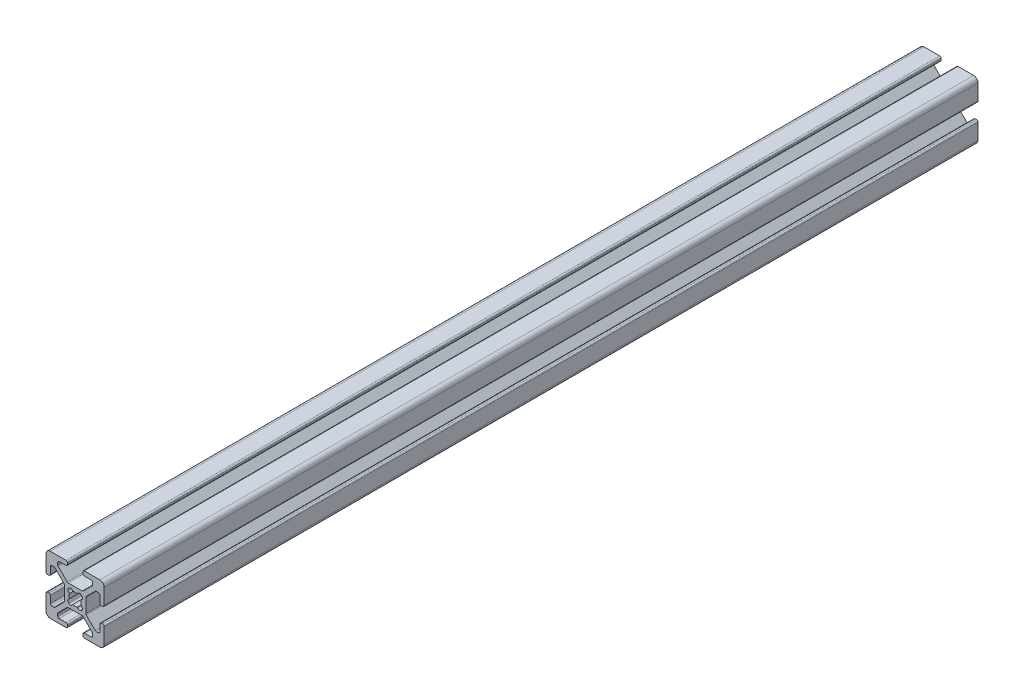
SolidWorks part; units mm, degrees
material "6063-O, Barre extrudée (SS)"
ref_plane "Front Plane" through (0, 0, 0) normal (0, 0, 1) x (1, 0, 0)
ref_plane "Top Plane" through (0, 0, 0) normal (0, 1, 0) x (1, 0, 0)
ref_plane "Right Plane" through (0, 0, 0) normal (1, 0, 0) x (0, 0, -1)
sketch "Sketch1" plane through (0, 0, 0) normal (0, 0, 1) x (1, 0, 0)
  line L0 (-5.0323, -0.3411) -> (-5.5163, -0.3411)
  line L1 (-6.0243, 0.1669) -> (-6.0243, 2.5159)
  line L2 (-4.5243, 0.1669) -> (-4.5243, 5.5289)
  line L3 (-10.8693, -5.355) -> (-10.8693, -0.5871)
  line L4 (-7.2582, 3.0239) -> (-6.5323, 3.0239)
  line L5 (-7.6174, 2.8752) -> (-10.7205, -0.2279)
  line L6 (-5.0323, -5.6011) -> (-5.5163, -5.6011)
  line L7 (-4.5243, -6.1091) -> (-4.5243, -11.4711)
  line L8 (-6.0243, -6.1091) -> (-6.0243, -8.4581)
  line L9 (-7.2582, -8.9661) -> (-6.5323, -8.9661)
  line L10 (-7.6174, -8.8173) -> (-10.7205, -5.7142)
  line L11 (-12.3994, -5.2756) -> (-12.2198, -5.096)
  line L12 (-17.1543, 6.5209) -> (-17.1543, 6.0369)
  line L13 (-17.6623, 7.0289) -> (-23.0243, 7.0289)
  line L14 (-17.6623, 5.5289) -> (-20.0113, 5.5289)
  line L15 (-12.1404, 0.6839) -> (-16.9082, 0.6839)
  line L16 (-20.5193, 4.295) -> (-20.5193, 5.0209)
  line L17 (-20.3705, 3.9358) -> (-17.2674, 0.8327)
  line L18 (-11.8943, 6.5209) -> (-11.8943, 6.0369)
  line L19 (-11.3863, 7.0289) -> (-6.0243, 7.0289)
  line L20 (-11.3863, 5.5289) -> (-9.0373, 5.5289)
  line L21 (-8.5293, 4.295) -> (-8.5293, 5.0209)
  line L22 (-8.6781, 3.9358) -> (-11.7812, 0.8327)
  line L23 (-12.2198, -0.8462) -> (-12.3994, -0.6666)
  line L24 (-24.0163, -5.6011) -> (-23.5323, -5.6011)
  line L25 (-24.5243, -6.1091) -> (-24.5243, -11.4711)
  line L26 (-23.0243, -6.1091) -> (-23.0243, -8.4581)
  line L27 (-18.1793, -0.5871) -> (-18.1793, -5.355)
  line L28 (-21.7904, -8.9661) -> (-22.5163, -8.9661)
  line L29 (-21.4312, -8.8173) -> (-18.3281, -5.7142)
  line L30 (-24.0163, -0.3411) -> (-23.5323, -0.3411)
  line L31 (-24.5243, 0.1669) -> (-24.5243, 5.5289)
  line L32 (-23.0243, 0.1669) -> (-23.0243, 2.5159)
  line L33 (-21.7904, 3.0239) -> (-22.5163, 3.0239)
  line L34 (-21.4312, 2.8752) -> (-18.3281, -0.2279)
  line L35 (-16.6492, -0.6666) -> (-16.8288, -0.8462)
  line L36 (-11.8943, -12.4631) -> (-11.8943, -11.9791)
  line L37 (-11.3863, -12.9711) -> (-6.0243, -12.9711)
  line L38 (-11.3863, -11.4711) -> (-9.0373, -11.4711)
  line L39 (-16.9082, -6.6261) -> (-12.1404, -6.6261)
  line L40 (-8.5293, -10.2371) -> (-8.5293, -10.9631)
  line L41 (-8.6781, -9.8779) -> (-11.7812, -6.7748)
  line L42 (-17.1543, -12.4631) -> (-17.1543, -11.9791)
  line L43 (-17.6623, -12.9711) -> (-23.0243, -12.9711)
  line L44 (-17.6623, -11.4711) -> (-20.0113, -11.4711)
  line L45 (-20.5193, -10.2371) -> (-20.5193, -10.9631)
  line L46 (-20.3705, -9.8779) -> (-17.2674, -6.7748)
  line L47 (-16.8288, -5.096) -> (-16.6492, -5.2756)
  arc A0 (-15.3283, -4.9062) -> (-13.7203, -4.9062) centre (-14.5243, -2.9711) ccw
  arc A1 (-6.0243, 2.5159) -> (-6.5323, 3.0239) centre (-6.5323, 2.5159) ccw
  arc A2 (-7.2582, 3.0239) -> (-7.6174, 2.8752) centre (-7.2582, 2.5159) ccw
  arc A3 (-10.7205, -0.2279) -> (-10.8693, -0.5871) centre (-10.3613, -0.5871) ccw
  arc A4 (-10.8693, -5.355) -> (-10.7205, -5.7142) centre (-10.3613, -5.355) ccw
  arc A5 (-7.6174, -8.8173) -> (-7.2582, -8.9661) centre (-7.2582, -8.4581) ccw
  arc A6 (-6.5323, -8.9661) -> (-6.0243, -8.4581) centre (-6.5323, -8.4581) ccw
  arc A7 (-5.5163, -5.6011) -> (-6.0243, -6.1091) centre (-5.5163, -6.1091) ccw
  arc A8 (-4.5243, -6.1091) -> (-5.0323, -5.6011) centre (-5.0323, -6.1091) ccw
  arc A9 (-5.0323, -0.3411) -> (-4.5243, 0.1669) centre (-5.0323, 0.1669) ccw
  arc A10 (-6.0243, 0.1669) -> (-5.5163, -0.3411) centre (-5.5163, 0.1669) ccw
  arc A11 (-13.7203, -4.9062) -> (-12.3994, -5.2756) centre (-12.9559, -4.7191) ccw
  arc A12 (-12.2198, -5.096) -> (-12.5892, -3.775) centre (-12.7763, -4.5395) ccw
  arc A13 (-17.1543, 6.5209) -> (-17.6623, 7.0289) centre (-17.6623, 6.5209) ccw
  arc A14 (-17.6623, 5.5289) -> (-17.1543, 6.0369) centre (-17.6623, 6.0369) ccw
  arc A15 (-12.5892, -3.775) -> (-12.5892, -2.1671) centre (-14.5243, -2.9711) ccw
  arc A16 (-17.2674, 0.8327) -> (-16.9082, 0.6839) centre (-16.9082, 1.1919) ccw
  arc A17 (-20.0113, 5.5289) -> (-20.5193, 5.0209) centre (-20.0113, 5.0209) ccw
  arc A18 (-20.5193, 4.295) -> (-20.3705, 3.9358) centre (-20.0113, 4.295) ccw
  arc A19 (-11.8943, 6.0369) -> (-11.3863, 5.5289) centre (-11.3863, 6.0369) ccw
  arc A20 (-11.3863, 7.0289) -> (-11.8943, 6.5209) centre (-11.3863, 6.5209) ccw
  arc A21 (-8.5293, 5.0209) -> (-9.0373, 5.5289) centre (-9.0373, 5.0209) ccw
  arc A22 (-8.6781, 3.9358) -> (-8.5293, 4.295) centre (-9.0373, 4.295) ccw
  arc A23 (-12.1404, 0.6839) -> (-11.7812, 0.8327) centre (-12.1404, 1.1919) ccw
  arc A24 (-12.5892, -2.1671) -> (-12.2198, -0.8462) centre (-12.7763, -1.4027) ccw
  arc A25 (-12.3994, -0.6666) -> (-13.7203, -1.0359) centre (-12.9559, -1.223) ccw
  arc A26 (-24.0163, -5.6011) -> (-24.5243, -6.1091) centre (-24.0163, -6.1091) ccw
  arc A27 (-23.0243, -6.1091) -> (-23.5323, -5.6011) centre (-23.5323, -6.1091) ccw
  arc A28 (-13.7203, -1.0359) -> (-15.3283, -1.0359) centre (-14.5243, -2.9711) ccw
  arc A29 (-18.3281, -5.7142) -> (-18.1793, -5.355) centre (-18.6873, -5.355) ccw
  arc A30 (-23.0243, -8.4581) -> (-22.5163, -8.9661) centre (-22.5163, -8.4581) ccw
  arc A31 (-21.7904, -8.9661) -> (-21.4312, -8.8173) centre (-21.7904, -8.4581) ccw
  arc A32 (-23.5323, -0.3411) -> (-23.0243, 0.1669) centre (-23.5323, 0.1669) ccw
  arc A33 (-24.5243, 0.1669) -> (-24.0163, -0.3411) centre (-24.0163, 0.1669) ccw
  arc A34 (-22.5163, 3.0239) -> (-23.0243, 2.5159) centre (-22.5163, 2.5159) ccw
  arc A35 (-21.4312, 2.8752) -> (-21.7904, 3.0239) centre (-21.7904, 2.5159) ccw
  arc A36 (-18.1793, -0.5871) -> (-18.3281, -0.2279) centre (-18.6873, -0.5871) ccw
  arc A37 (-15.3283, -1.0359) -> (-16.6492, -0.6666) centre (-16.0927, -1.223) ccw
  arc A38 (-16.8288, -0.8462) -> (-16.4594, -2.1671) centre (-16.2723, -1.4027) ccw
  arc A39 (-11.8943, -12.4631) -> (-11.3863, -12.9711) centre (-11.3863, -12.4631) ccw
  arc A40 (-11.3863, -11.4711) -> (-11.8943, -11.9791) centre (-11.3863, -11.9791) ccw
  arc A41 (-16.4594, -2.1671) -> (-16.4594, -3.775) centre (-14.5243, -2.9711) ccw
  arc A42 (-11.7812, -6.7748) -> (-12.1404, -6.6261) centre (-12.1404, -7.1341) ccw
  arc A43 (-9.0373, -11.4711) -> (-8.5293, -10.9631) centre (-9.0373, -10.9631) ccw
  arc A44 (-8.5293, -10.2371) -> (-8.6781, -9.8779) centre (-9.0373, -10.2371) ccw
  arc A45 (-17.1543, -11.9791) -> (-17.6623, -11.4711) centre (-17.6623, -11.9791) ccw
  arc A46 (-17.6623, -12.9711) -> (-17.1543, -12.4631) centre (-17.6623, -12.4631) ccw
  arc A47 (-20.5193, -10.9631) -> (-20.0113, -11.4711) centre (-20.0113, -10.9631) ccw
  arc A48 (-20.3705, -9.8779) -> (-20.5193, -10.2371) centre (-20.0113, -10.2371) ccw
  arc A49 (-16.9082, -6.6261) -> (-17.2674, -6.7748) centre (-16.9082, -7.1341) ccw
  arc A50 (-16.4594, -3.775) -> (-16.8288, -5.096) centre (-16.2723, -4.5395) ccw
  arc A51 (-16.6492, -5.2756) -> (-15.3283, -4.9062) centre (-16.0927, -4.7191) ccw
  arc A52 (-4.5243, 5.5289) -> (-6.0243, 7.0289) centre (-6.0243, 5.5289) ccw
  arc A53 (-6.0243, -12.9711) -> (-4.5243, -11.4711) centre (-6.0243, -11.4711) ccw
  arc A54 (-24.5243, -11.4711) -> (-23.0243, -12.9711) centre (-23.0243, -11.4711) ccw
  arc A55 (-23.0243, 7.0289) -> (-24.5243, 5.5289) centre (-23.0243, 5.5289) ccw
extrude "Extrude1" add sketch "Sketch1" along normal blind 300
